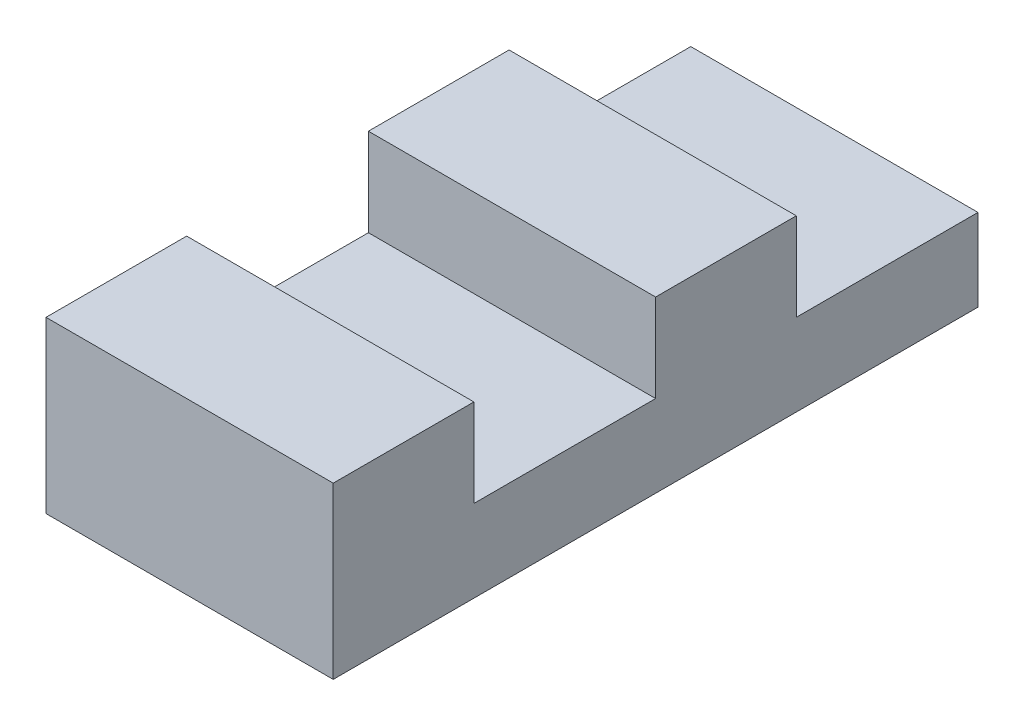
SolidWorks part; units mm, degrees
ref_plane "Front Plane" through (0, 0, 0) normal (0, 0, 1) x (1, 0, 0)
ref_plane "Top Plane" through (0, 0, 0) normal (0, 1, 0) x (1, 0, 0)
ref_plane "Right Plane" through (0, 0, 0) normal (1, 0, 0) x (0, 0, -1)
sketch "Sketch1" plane through (0, 0, 0) normal (1, 0, 0) x (0, 0, -1)
  line L1 (0, 0) -> (4.8, 0)
  line L2 (0, 0) -> (0, 5.8)
  line L3 (0, 5.8) -> (4.8, 5.8)
  line L4 (4.8, 2.8) -> (4.8, 5.8)
  line L5 (0, 0) -> (4.8, 5.8) construction
  line L6 (0, 5.8) -> (4.8, 0) construction
  line L7 (4.8, 0) -> (11, 0)
  line L9 (4.8, 2.8) -> (11, 2.8)
  line L10 (11, 0) -> (11, 2.8)
  line L11 (4.8, 0) -> (11, 2.8) construction
  line L12 (4.8, 2.8) -> (11, 0) construction
  point P4 (2.4, 2.9)
  point P9 (7.9, 1.4)
  point P10 (4.8, 0)
  point P11 (4.2052, 2.8)
  dimension "D1" = 5.8
  dimension "D2" = 4.8
  dimension "D3" = 2.8
  dimension "D4" = 11
extrude "Boss-Extrude1" add sketch "Sketch1" along normal blind 9.8
pattern_linear "LPattern1" count 2 spacing 11 along (0, 0, -1) of "Boss-Extrude1"
